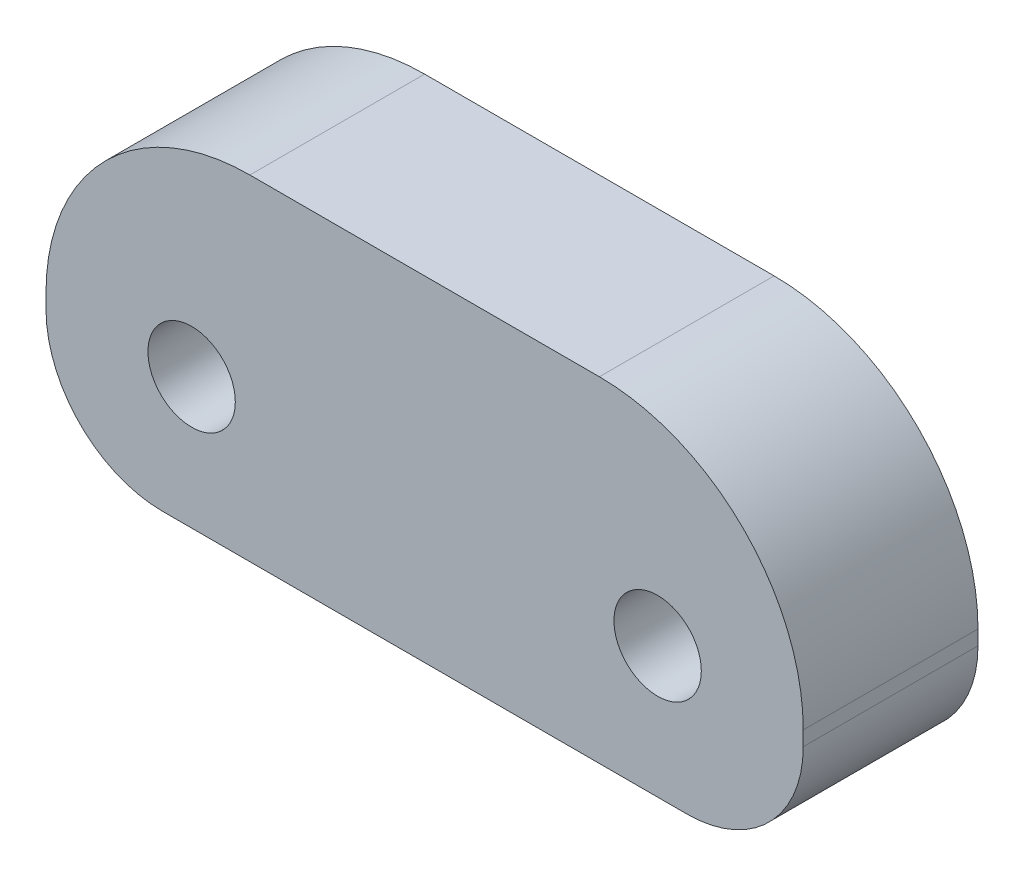
SolidWorks part; units mm, degrees
ref_plane "Plano frontal" through (0, 0, 0) normal (0, 0, 1) x (1, 0, 0)
ref_plane "Plano superior" through (0, 0, 0) normal (0, 1, 0) x (1, 0, 0)
ref_plane "Plano direito" through (0, 0, 0) normal (1, 0, 0) x (0, 0, -1)
sketch "Esboço1" plane through (0, 0, 0) normal (0, 0, 1) x (1, 0, 0)
  line L1 (-13, -5.75) -> (13, -5.75)
  line L2 (-13, -5.75) -> (-13, 5.75)
  line L3 (-13, 5.75) -> (13, 5.75)
  line L4 (13, -5.75) -> (13, 5.75)
  line L5 (0, 5.75) -> (0, -5.75) construction
  line L6 (-13, 0) -> (13, 0) construction
  circle A0 centre (-8, -1.25) radius 1.5
  circle A1 centre (8, -1.25) radius 1.5
  point P0 (0, 0)
  point P8 (-8, -1.4107)
  dimension "D1" = 3
  dimension "D4" = 16
  dimension "D2" = 5
  dimension "D3" = 11.5
  dimension "D5" = 7
extrude "Ressalto-extrusão1" add sketch "Esboço1" along normal blind 6 contours L1 L4 L3 L2 A0 A1
fillet "Filete1" radius 7 2 edges at (-13, 5.75, 3) (13, 5.75, 3)
fillet "Filete2" radius 4 2 edges at (13, -5.75, 3) (-13, -5.75, 3)
